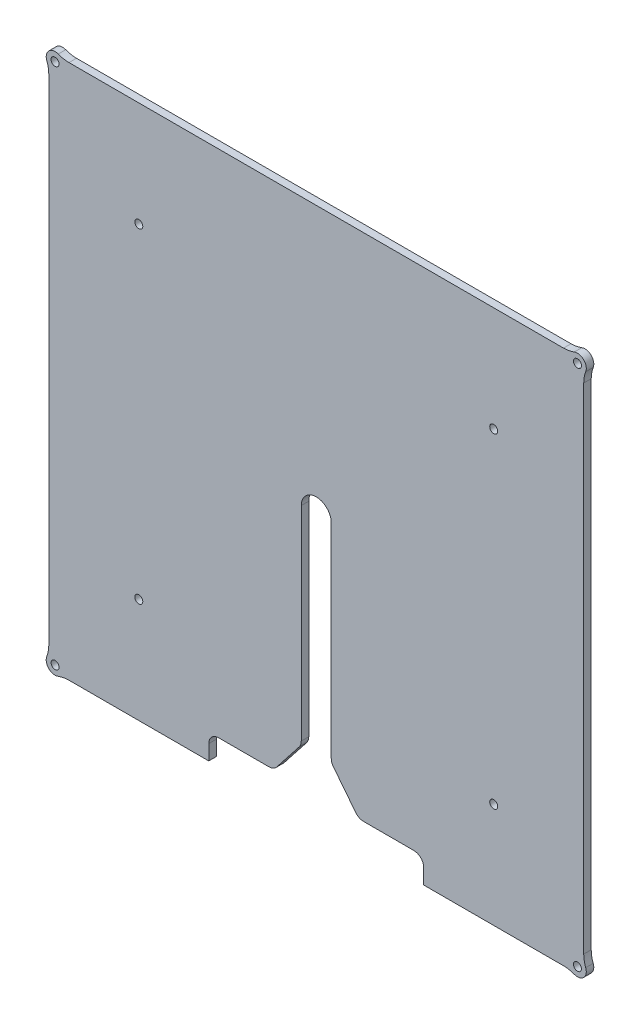
SolidWorks part; units mm, degrees
material "Balsa"
ref_plane "Front Plane" through (0, 0, 0) normal (0, 0, 1) x (1, 0, 0)
ref_plane "Top Plane" through (0, 0, 0) normal (0, 1, 0) x (1, 0, 0)
ref_plane "Right Plane" through (0, 0, 0) normal (1, 0, 0) x (0, 0, -1)
sketch "Sketch1" plane through (0, 0, 0) normal (0, 0, 1) x (1, 0, 0)
  line L0 (-107, 98.923) -> (-107, -98.923)
  line L1 (98.923, 107) -> (-98.923, 107)
  line L2 (107, -98.923) -> (107, 98.923)
  line L3 (43, -107) -> (98.923, -107)
  line L4 (43, -107) -> (43, -101)
  line L5 (39, -97) -> (-39, -97)
  line L6 (-43, -101) -> (-43, -107)
  line L7 (-98.923, -107) -> (-43, -107)
  line L9 (104.5, -104.5) -> (-104.5, -104.5) construction
  line L10 (104.5, -104.5) -> (104.5, 104.5) construction
  line L11 (104.5, 104.5) -> (-104.5, 104.5) construction
  line L12 (-104.5, -104.5) -> (-104.5, 104.5) construction
  line L13 (104.5, -104.5) -> (-104.5, 104.5) construction
  line L14 (104.5, 104.5) -> (-104.5, -104.5) construction
  circle A0 centre (-104.5, -104.5) radius 1.6
  circle A1 centre (-104.5, 104.5) radius 1.6
  circle A2 centre (104.5, 104.5) radius 1.6
  circle A3 centre (104.5, -104.5) radius 1.6
  arc A4 (43, -101) -> (39, -97) centre (39, -101) ccw
  arc A5 (-39, -97) -> (-43, -101) centre (-39, -101) ccw
  arc A6 (-103.2308, 107.7999) -> (-107.7999, 103.2308) centre (-104.5, 104.5) ccw
  arc A8 (-107.7999, -103.2308) -> (-103.2308, -107.7999) centre (-104.5, -104.5) ccw
  arc A9 (98.923, -107) -> (103.2308, -107.7999) centre (98.923, -119) cw
  arc A10 (103.2308, -107.7999) -> (107.7999, -103.2308) centre (104.5, -104.5) ccw
  arc A13 (107.7999, 103.2308) -> (103.2308, 107.7999) centre (104.5, 104.5) ccw
  arc A14 (107, -98.923) -> (107.7999, -103.2308) centre (119, -98.923) ccw
  arc A15 (-103.2308, -107.7999) -> (-98.923, -107) centre (-98.923, -119) cw
  arc A16 (-107, -98.923) -> (-107.7999, -103.2308) centre (-119, -98.923) cw
  arc A17 (-107.7999, 103.2308) -> (-107, 98.923) centre (-119, 98.923) cw
  arc A18 (-103.2308, 107.7999) -> (-98.923, 107) centre (-98.923, 119) ccw
  arc A19 (107, 98.923) -> (107.7999, 103.2308) centre (119, 98.923) cw
  arc A20 (103.2308, 107.7999) -> (98.923, 107) centre (98.923, 119) cw
  point P0 (0, 0)
  dimension "D1" = 12
  dimension "D3" = 12
  dimension "D4" = 12
  dimension "D5" = 12
  dimension "D6" = 12
  dimension "D7" = 12
  dimension "D2" = 209
  dimension "D8" = 214
  dimension "D9" = 10
extrude "Boss-Extrude1" add sketch "Sketch1" along normal blind 3
sketch "Sketch2" plane through (0, 0, 0) normal (0, 0, -1) x (-1, 0, 0)
  line L0 (39, -97) -> (-39, -97) construction
  line L1 (6, -97) -> (-6, -97)
  line L2 (6, -97) -> (6, 0)
  line L3 (6, 0) -> (-6, 0) construction
  line L4 (-6, -97) -> (-6, 0)
  line L5 (6, -97) -> (-6, 0) construction
  line L6 (6, 0) -> (-6, -97) construction
  arc A0 (6, 0) -> (-6, 0) centre (0, 0) ccw
  point P3 (0, -48.5)
  dimension "D1" = 6
extrude "Cut-Extrude1" cut sketch "Sketch2" against normal through all
sketch "Sketch4" plane through (0, 0, 3) normal (0, 0, 1) x (1, 0, 0)
  line L0 (-17, -97) -> (17, -97)
  line L1 (-39, -97) -> (-6, -97) construction
  line L2 (6, -97) -> (39, -97) construction
  line L3 (17, -97) -> (6, -83)
  line L4 (6, 0) -> (6, -97) construction
  line L5 (6, -83) -> (-6, -83)
  line L6 (-6, -97) -> (-6, 0) construction
  line L7 (-6, -83) -> (-17, -97)
  line L8 (-43, -107) -> (-43, -101) construction
  dimension "D1" = 26
  dimension "D2" = 14
extrude "Cut-Extrude3" cut sketch "Sketch4" against normal through all
fillet "Fillet1" radius 4 4 edges at (6, -83, 1.5) (-6, -83, 1.5) (17, -97, 1.5) (-17, -97, 1.5)
sketch "Sketch3" plane through (0, 0, 3) normal (0, 0, 1) x (1, 0, 0)
  line L0 (-107, 98.923) -> (-107, -98.923) construction
  line L1 (71, -65) -> (-71, -65) construction
  line L2 (71, -65) -> (71, 65) construction
  line L3 (71, 65) -> (-71, 65) construction
  line L4 (-71, -65) -> (-71, 65) construction
  line L5 (71, -65) -> (-71, 65) construction
  line L6 (71, 65) -> (-71, -65) construction
  circle A0 centre (-71, 65) radius 1.6
  circle A1 centre (71, 65) radius 1.6
  circle A2 centre (71, -65) radius 1.6
  circle A3 centre (-71, -65) radius 1.6
  point P0 (0, 0)
  dimension "D3" = 3.2
  dimension "D1" = 36
  dimension "D2" = 130
extrude "Cut-Extrude2" cut sketch "Sketch3" against normal through all
